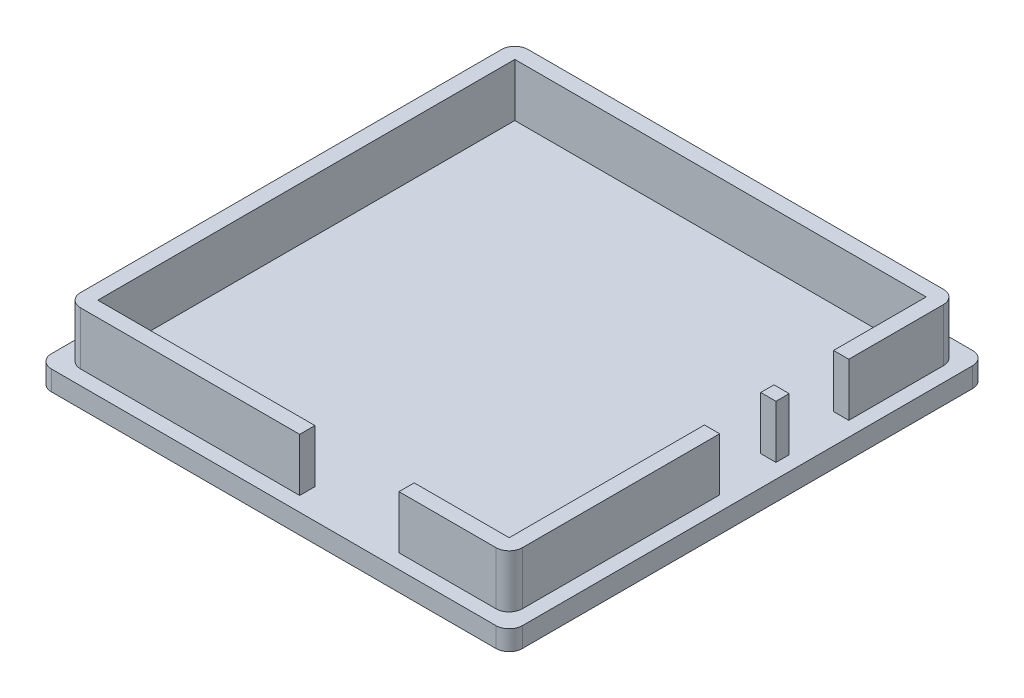
SolidWorks part; units mm, degrees
material "ABS"
ref_plane "Plano frontal" through (0, 0, 0) normal (0, 0, 1) x (1, 0, 0)
ref_plane "Plano superior" through (0, 0, 0) normal (0, 1, 0) x (1, 0, 0)
ref_plane "Plano direito" through (0, 0, 0) normal (1, 0, 0) x (0, 0, -1)
sketch "Esboço1" plane through (0, 0, 0) normal (0, 1, 0) x (1, 0, 0)
  line L1 (-35.575, -36) -> (35.575, -36)
  line L2 (-35.575, -36) -> (-35.575, 36)
  line L3 (-35.575, 36) -> (35.575, 36)
  line L4 (35.575, -36) -> (35.575, 36)
  line L5 (-35.575, -36) -> (35.575, 36) construction
  line L6 (-35.575, 36) -> (35.575, -36) construction
  point P0 (0, 0)
  dimension "D1" = 71.15
  dimension "D2" = 72
extrude "Ressalto-extrusão1" add sketch "Esboço1" along normal mid plane 3
sketch "Esboço2" plane through (0, 1.5, 0) normal (0, 1, 0) x (1, 0, 0)
  line L8 (33.375, -33.8) -> (33.375, 33.8)
  line L9 (33.375, 33.8) -> (-33.375, 33.8)
  line L10 (-33.375, 33.8) -> (-33.375, -33.8)
  line L11 (-33.375, -33.8) -> (33.375, -33.8)
  line L12 (33.375, -33.8) -> (33.375, 33.8)
  line L13 (33.375, 33.8) -> (-33.375, 33.8)
  line L14 (-33.375, 33.8) -> (-33.375, -33.8)
  line L15 (-33.375, -33.8) -> (33.375, -33.8)
  line L20 (31.075, -31.5) -> (31.075, 31.5)
  line L21 (31.075, 31.5) -> (-31.075, 31.5)
  line L22 (-31.075, 31.5) -> (-31.075, -31.5)
  line L23 (-31.075, -31.5) -> (31.075, -31.5)
  line L24 (31.075, -31.5) -> (31.075, 31.5)
  line L25 (31.075, 31.5) -> (-31.075, 31.5)
  line L26 (-31.075, 31.5) -> (-31.075, -31.5)
  line L27 (-31.075, -31.5) -> (31.075, -31.5)
  dimension "D1" = 2.2
  dimension "D2" = 4.5
extrude "Ressalto-extrusão2" add sketch "Esboço2" along normal blind 8 contours L12 L13 L14 L15 | L24 L25 L26 L27
fillet "Filete1" radius 2 8 edges at (35.575, 0, 36) (33.375, 5.5, 33.8) (35.575, 0, -36) (33.375, 5.5, -33.8) (-35.575, 0, -36) (-33.375, 5.5, -33.8) (-33.375, 5.5, 33.8) (-35.575, 0, 36)
sketch "Esboço3" plane through (31.075, 0, 0) normal (-1, 0, 0) x (0, 0, 1)
  line L0 (31.5, 9.5) -> (-31.5, 9.5) construction
  line L1 (-17.5, 1.5) -> (-8.5, 1.5)
  line L2 (-17.5, 1.5) -> (-17.5, 9.5)
  line L3 (-17.5, 9.5) -> (-8.5, 9.5)
  line L4 (-8.5, 1.5) -> (-8.5, 9.5)
  line L5 (-17.5, 1.5) -> (-8.5, 9.5) construction
  line L6 (-17.5, 9.5) -> (-8.5, 1.5) construction
  line L7 (31.5, 1.5) -> (-31.5, 1.5) construction
  line L8 (-31.5, 9.5) -> (-31.5, 1.5) construction
  point P0 (-13, 5.5)
  dimension "D1" = 14
  dimension "D2" = 9
extrude "Corte-extrusão1" cut sketch "Esboço3" against normal up to surface (4.5 mm away) up to face at (35.575, 0, 0)
sketch "Esboço4" plane through (31.075, 0, 0) normal (-1, 0, 0) x (0, 0, 1)
  line L0 (31.5, 1.5) -> (-8.5, 1.5) construction
  line L1 (-6.5, 1.5) -> (2, 1.5)
  line L2 (-6.5, 1.5) -> (-6.5, 9.5)
  line L3 (-6.5, 9.5) -> (2, 9.5)
  line L4 (2, 1.5) -> (2, 9.5)
  line L5 (31.5, 9.5) -> (-8.5, 9.5) construction
  line L6 (-31.5, 9.5) -> (-31.5, 1.5) construction
  dimension "D1" = 25
  dimension "D2" = 8.5
extrude "Corte-extrusão2" cut sketch "Esboço4" against normal up to surface (4.5 mm away) up to face at (35.575, 0, 0)
sketch "Esboço5" plane through (0, 0, 31.5) normal (0, 0, -1) x (-1, 0, 0)
  line L0 (31.075, 1.5) -> (-31.075, 1.5) construction
  line L1 (-16.725, 1.5) -> (-1.725, 1.5)
  line L2 (-16.725, 1.5) -> (-16.725, 9.5)
  line L3 (-16.725, 9.5) -> (-1.725, 9.5)
  line L4 (-1.725, 1.5) -> (-1.725, 9.5)
  line L5 (31.075, 9.5) -> (-31.075, 9.5) construction
  line L6 (-31.075, 9.5) -> (-31.075, 1.5) construction
  dimension "D1" = 29.35
  dimension "D2" = 15
extrude "Corte-extrusão3" cut sketch "Esboço5" against normal up to surface (4.5 mm away) up to face at (0, 0, 36)
